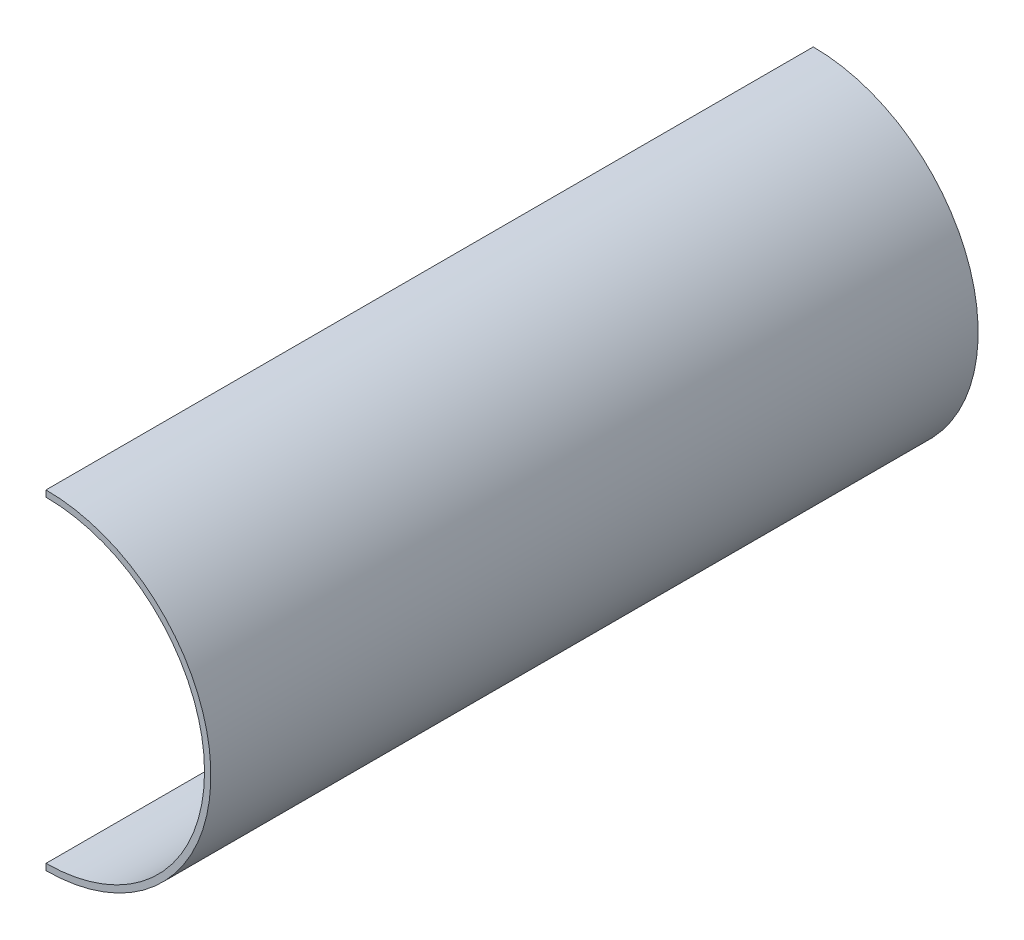
SolidWorks part; units mm, degrees
ref_plane "前视基准面" through (0, 0, 0) normal (0, 0, 1) x (1, 0, 0)
ref_plane "上视基准面" through (0, 0, 0) normal (0, 1, 0) x (1, 0, 0)
ref_plane "右视基准面" through (0, 0, 0) normal (1, 0, 0) x (0, 0, -1)
sketch "草图1" plane through (0, 0, 0) normal (0, 0, 1) x (1, 0, 0)
  line L0 (50, 52) -> (50, 50)
  line L6 (50, -50) -> (50, -52)
  arc A3 (100, 0) -> (75, -43.3013) centre (50, 0) cw
  arc A4 (76, -45.0333) -> (102, 0) centre (50, 0) ccw
  arc A5 (100, 0) -> (75, 43.3013) centre (50, 0) ccw
  arc A6 (102, 0) -> (76, 45.0333) centre (50, 0) ccw
  arc A7 (75, 43.3013) -> (50, 50) centre (50, 0) ccw
  arc A8 (76, 45.0333) -> (50, 52) centre (50, 0) ccw
  arc A9 (75, -43.3013) -> (50, -50) centre (50, 0) cw
  arc A10 (50, -52) -> (76, -45.0333) centre (50, 0) ccw
extrude "凸台-拉伸1" add sketch "草图1" along normal blind 242
ref_plane "基准面1" through (0, 0, 2) normal (0, 0, -1) x (-1, 0, 0)
sketch "草图4" plane through (0, 0, 2) normal (0, 0, -1) x (-1, 0, 0)
  line L0 (-50, 50) -> (-50, 48)
  line L5 (-50, -48) -> (-50, -50)
  arc A3 (-50, -48) -> (-50, 48) centre (-50, 0) cw
  arc A4 (-50, 50) -> (-50, -50) centre (-50, 0) ccw
  arc A5 (-50, 50) -> (-50, -50) centre (-50, 0) ccw construction
extrude "凸台-拉伸3" add sketch "草图4" against normal blind 1
